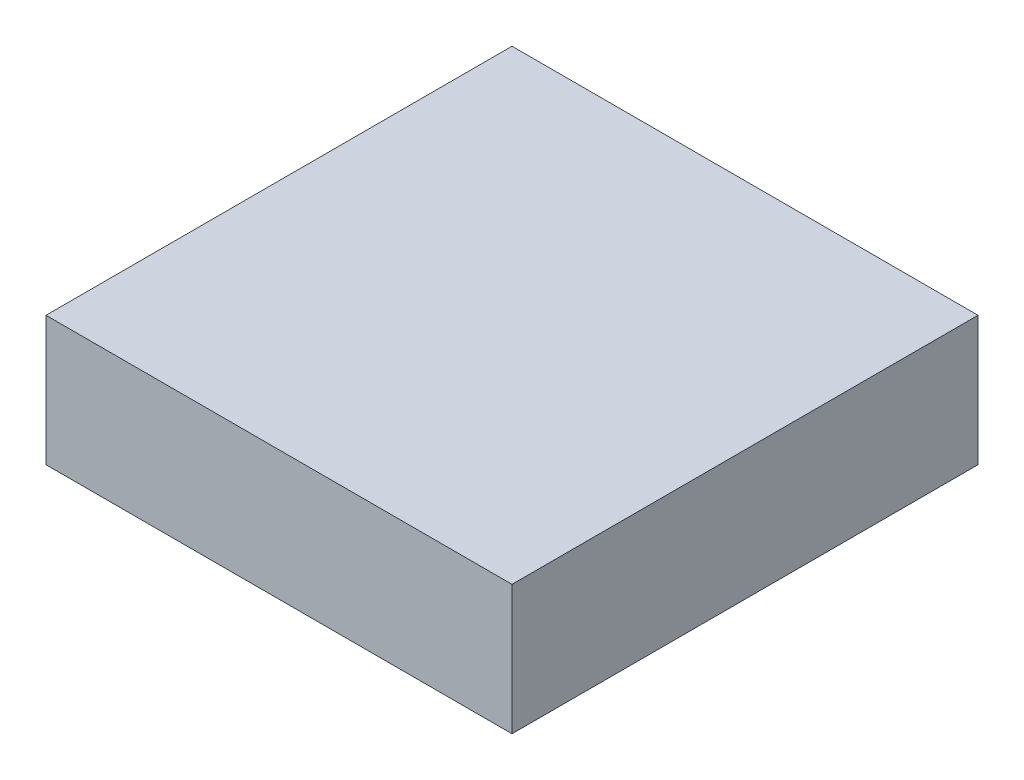
SolidWorks part; units mm, degrees
ref_plane "Front Plane" through (0, 0, 0) normal (0, 0, 1) x (1, 0, 0)
ref_plane "Top Plane" through (0, 0, 0) normal (0, 1, 0) x (1, 0, 0)
ref_plane "Right Plane" through (0, 0, 0) normal (1, 0, 0) x (0, 0, -1)
sketch "Sketch1" plane through (0, 0, 0) normal (0, 1, 0) x (1, 0, 0)
  line L0 (0, 18) -> (0, -18) construction
  line L1 (-18, -18) -> (18, -18)
  line L2 (-18, -18) -> (-18, 18)
  line L3 (-18, 18) -> (18, 18)
  line L4 (18, -18) -> (18, 18)
  line L5 (18, 0) -> (-18, 0) construction
  point P8 (0, 0)
  dimension "D1" = 36
extrude "Boss-Extrude1" add sketch "Sketch1" along normal blind 10
